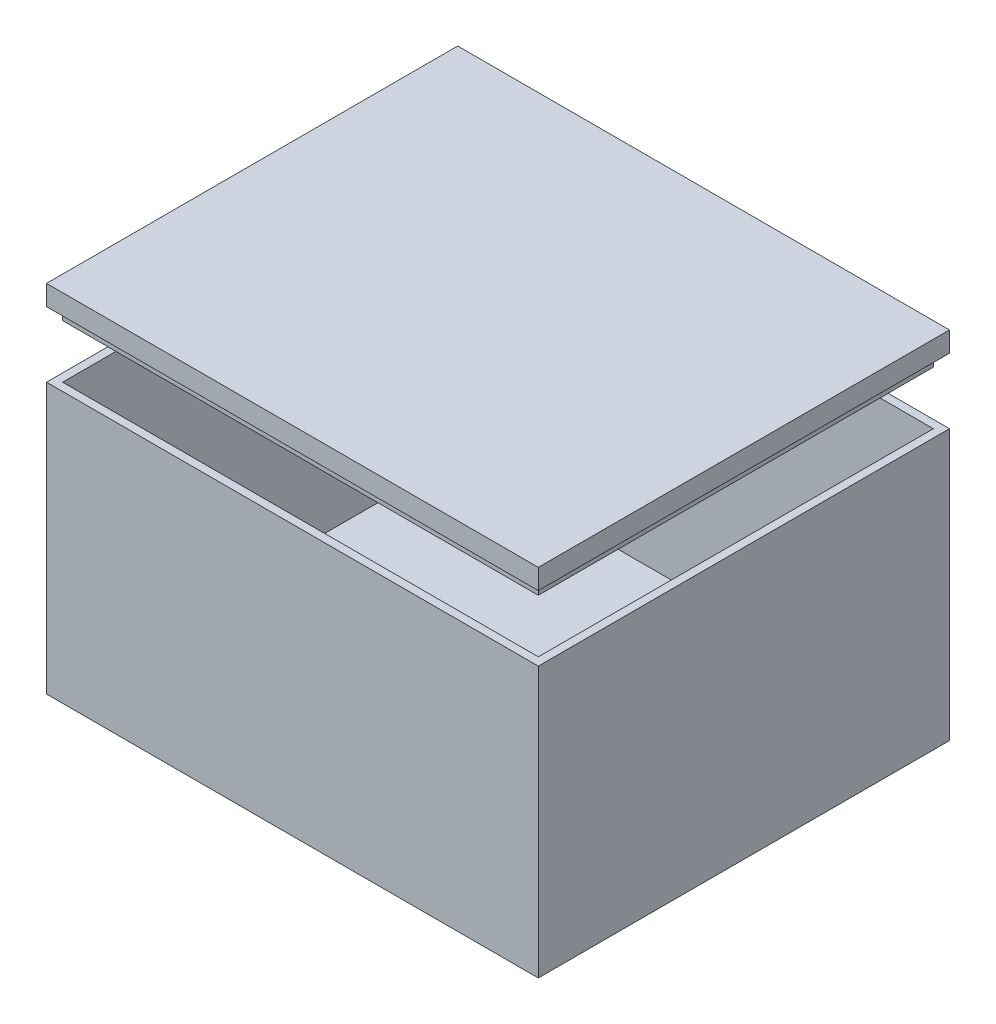
SolidWorks part; units mm, degrees
ref_plane "Front Plane" through (0, 0, 0) normal (0, 0, 1) x (1, 0, 0)
ref_plane "Top Plane" through (0, 0, 0) normal (0, 1, 0) x (1, 0, 0)
ref_plane "Right Plane" through (0, 0, 0) normal (1, 0, 0) x (0, 0, -1)
sketch "Sketch2" plane through (0, 0, 0) normal (0, 1, 0) x (1, 0, 0)
  line L1 (-54.5233, 28.1136) -> (67.4767, 28.1136)
  line L2 (-54.5233, 28.1136) -> (-54.5233, -73.8864)
  line L3 (-54.5233, -73.8864) -> (67.4767, -73.8864)
  line L4 (67.4767, 28.1136) -> (67.4767, -73.8864)
  dimension "D1" = 122
  dimension "D2" = 102
extrude "Boss-Extrude1" add sketch "Sketch2" along normal blind 67
shell "Shell2" thickness 2
sketch "Sketch7" plane through (0, 67, 0) normal (0, 1, 0) x (1, 0, 0)
  line L4 (-54.5233, 28.1136) -> (-54.5233, -73.8864)
  line L5 (-54.5233, -73.8864) -> (67.4767, -73.8864)
  line L6 (67.4767, -73.8864) -> (67.4767, 28.1136)
  line L7 (67.4767, 28.1136) -> (-54.5233, 28.1136)
  line L8 (-54.5233, 28.1136) -> (-54.5233, -73.8864)
  line L9 (-54.5233, -73.8864) -> (67.4767, -73.8864)
  line L10 (67.4767, -73.8864) -> (67.4767, 28.1136)
  line L11 (67.4767, 28.1136) -> (-54.5233, 28.1136)
  dimension "D1" = 0
extrude "Boss-Extrude3" add sketch "Sketch7" along normal blind 5 separate body
sketch "Sketch8" plane through (0, 67, 0) normal (0, -1, 0) x (1, 0, 0)
  line L8 (-52.5233, -26.1136) -> (65.4767, -26.1136)
  line L9 (65.4767, -26.1136) -> (65.4767, 71.8864)
  line L10 (65.4767, 71.8864) -> (-52.5233, 71.8864)
  line L11 (-52.5233, 71.8864) -> (-52.5233, -26.1136)
  line L12 (-52.5233, -26.1136) -> (65.4767, -26.1136)
  line L13 (65.4767, -26.1136) -> (65.4767, 71.8864)
  line L14 (65.4767, 71.8864) -> (-52.5233, 71.8864)
  line L15 (-52.5233, 71.8864) -> (-52.5233, -26.1136)
  dimension "D1" = 2
extrude "Extrude-Thin1" add sketch "Sketch8" along normal blind 3 thin thin type one direction reverse wall 2
move or copy body "Body-Move/Copy1" bodies to move or copy 104 copy no translate (0, 16.2233, 0)
split "Split1" bodies to split 101 105 resulting bodies 106 107
